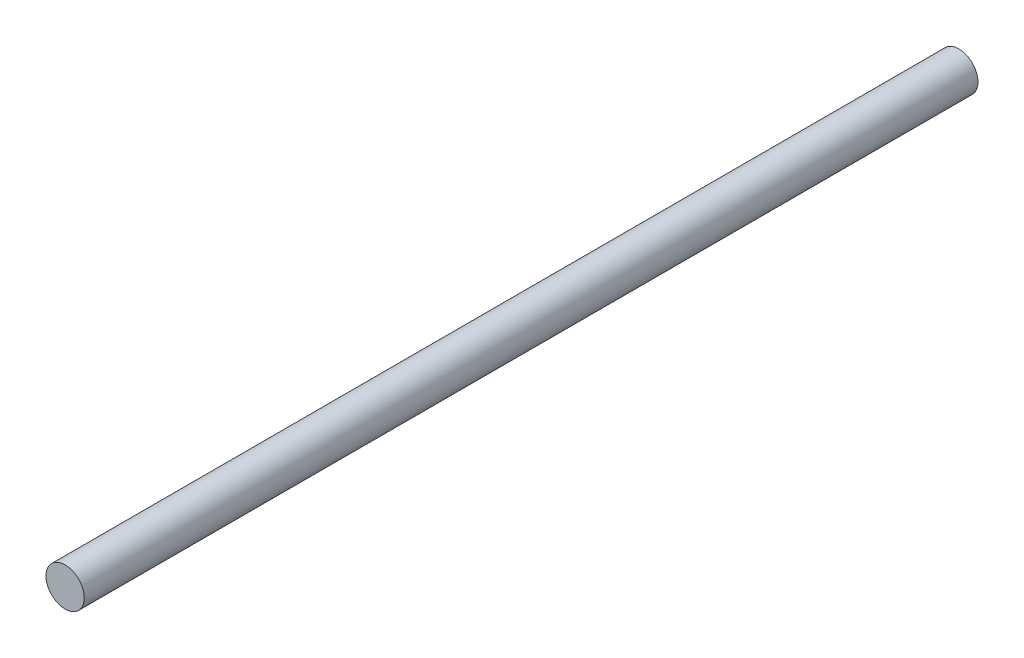
SolidWorks part; units mm, degrees
ref_plane "Alzado" through (0, 0, 0) normal (0, 0, 1) x (1, 0, 0)
ref_plane "Planta" through (0, 0, 0) normal (0, 1, 0) x (1, 0, 0)
ref_plane "Vista lateral" through (0, 0, 0) normal (1, 0, 0) x (0, 0, -1)
sketch "Croquis1" plane through (0, 0, 0) normal (0, 0, 1) x (1, 0, 0)
  circle A0 centre (0, 0) radius 7.5
  dimension "D1" = 15
extrude "Saliente-Extruir1" add sketch "Croquis1" along normal blind 350
